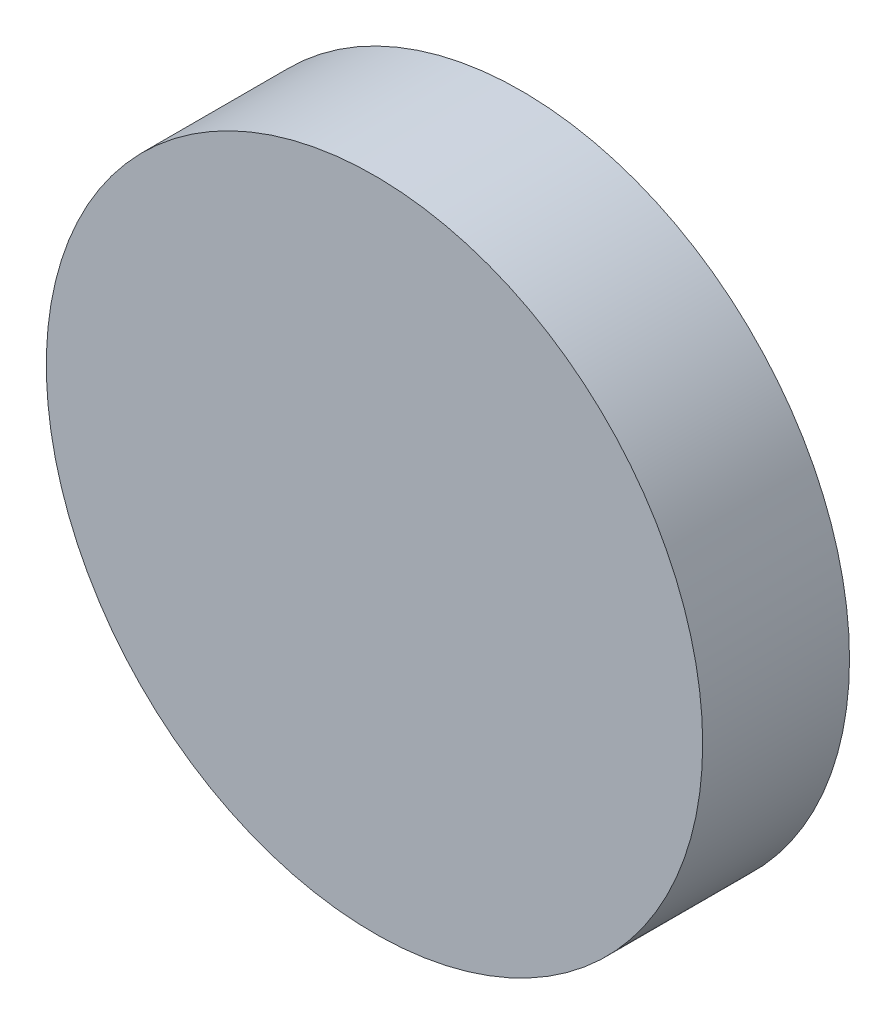
SolidWorks part; units mm, degrees
ref_plane "Ön Düzlem" through (0, 0, 0) normal (0, 0, 1) x (1, 0, 0)
ref_plane "Üst Düzlem" through (0, 0, 0) normal (0, 1, 0) x (1, 0, 0)
ref_plane "Sağ Düzlem" through (0, 0, 0) normal (1, 0, 0) x (0, 0, -1)
sketch "Çizim3" plane through (0, 0, 0) normal (0, 0, 1) x (1, 0, 0)
  circle A0 centre (0, 0) radius 380
extrude "Yükseklik-Ekstrüzyon3" add sketch "Çizim3" along normal blind 170
scale "Scale1" bodies to scale 103 scale about centroid uniform scaling yes scale factor 0.5
